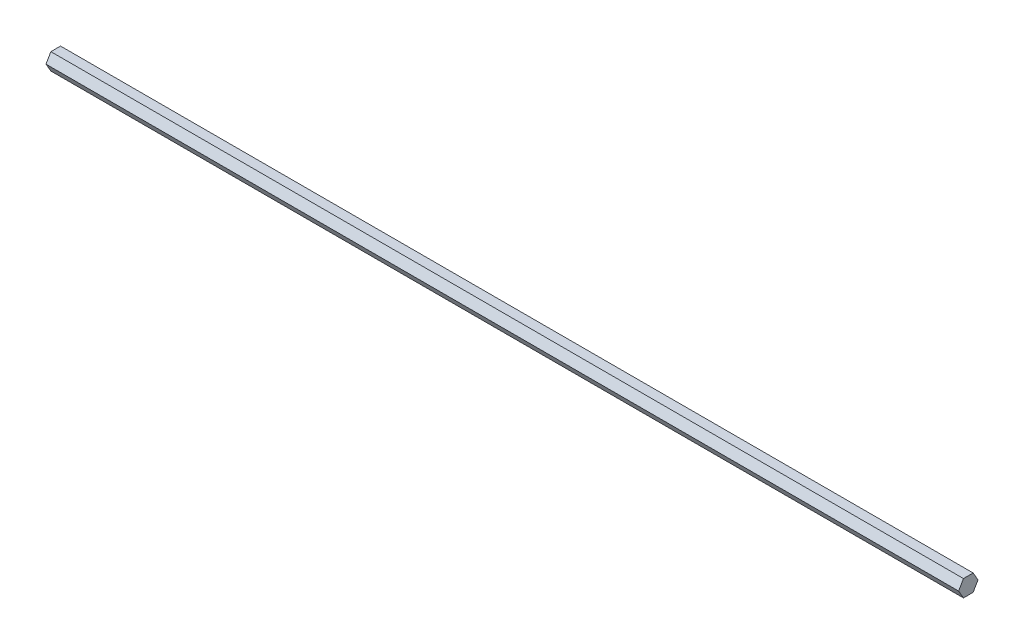
SolidWorks part; units mm, degrees
material "1060 Alloy"
ref_plane "Front Plane" through (0, 0, 0) normal (0, 0, 1) x (1, 0, 0)
ref_plane "Top Plane" through (0, 0, 0) normal (0, 1, 0) x (1, 0, 0)
ref_plane "Right Plane" through (0, 0, 0) normal (1, 0, 0) x (0, 0, -1)
sketch "Sketch1" plane through (0, 0, 0) normal (1, 0, 0) x (0, 0, -1)
  line L1 (7.3323, 0) -> (3.6662, 6.35)
  line L2 (3.6662, 6.35) -> (-3.6662, 6.35)
  line L3 (-3.6662, 6.35) -> (-7.3323, 0)
  line L4 (-7.3323, 0) -> (-3.6662, -6.35)
  line L5 (-3.6662, -6.35) -> (3.6662, -6.35)
  line L6 (3.6662, -6.35) -> (7.3323, 0)
  circle A0 centre (0, 0) radius 6.35 construction
  dimension "D1" = 12.7
extrude "Boss-Extrude1" add sketch "Sketch1" along normal blind 690.372
